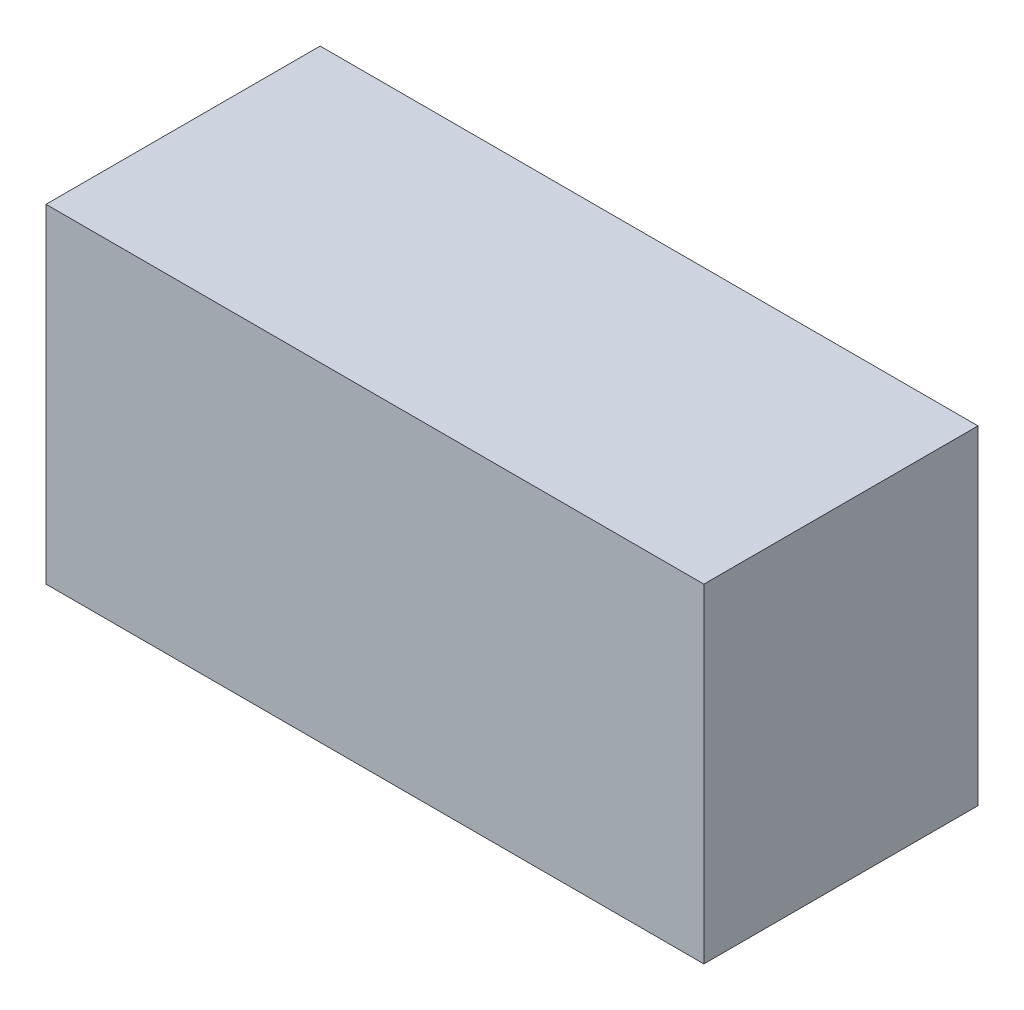
SolidWorks part; units mm, degrees
ref_plane "Front Plane" through (0, 0, 0) normal (0, 0, 1) x (1, 0, 0)
ref_plane "Top Plane" through (0, 0, 0) normal (0, 1, 0) x (1, 0, 0)
ref_plane "Right Plane" through (0, 0, 0) normal (1, 0, 0) x (0, 0, -1)
other "Center of Mass"
sketch "Sketch1" plane through (0, 0, 0) normal (1, 0, 0) x (0, 0, -1)
  line L1 (0, 0) -> (125, 0)
  line L2 (0, 0) -> (0, 150)
  line L3 (0, 150) -> (125, 150)
  line L4 (125, 0) -> (125, 150)
  dimension "D1" = 125
  dimension "D2" = 150
extrude "Boss-Extrude1" add sketch "Sketch1" along normal blind 300
ref_plane "CG plane" through (150, 0, 0) normal (-1, 0, 0) x (0, 0, 1)
equation "\"length\"= 300"
equation "\"height\"=150"
equation "\"D1@Sketch1\"=\"width\""
equation "\"width\"=125"
equation "\"D2@Sketch1\"=\"height\""
equation "\"D1@Boss-Extrude1\"=\"length\""
